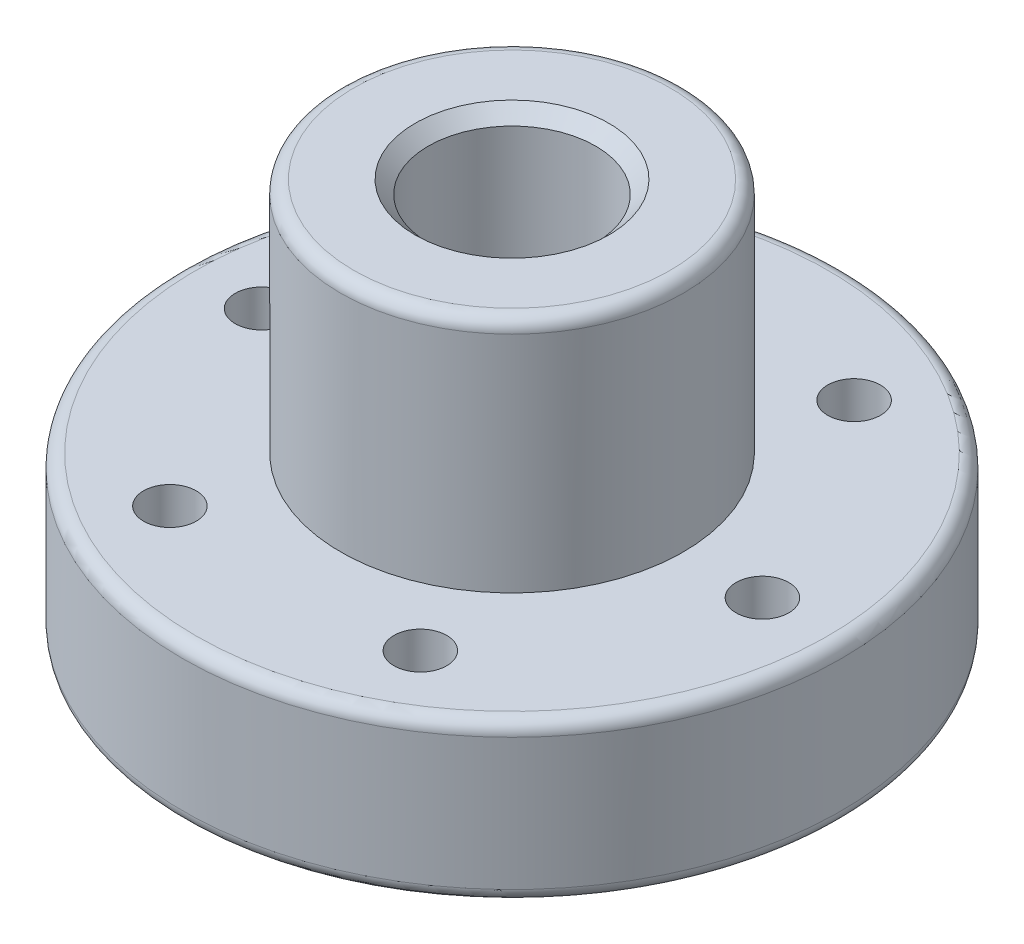
SolidWorks part; units mm, degrees
material "AISI 1035 Acier (SS)"
ref_plane "Plan de face" through (0, 0, 0) normal (0, 0, 1) x (1, 0, 0)
ref_plane "Plan de dessus" through (0, 0, 0) normal (0, 1, 0) x (1, 0, 0)
ref_plane "Plan de droite" through (0, 0, 0) normal (1, 0, 0) x (0, 0, -1)
sketch "Esquisse1" plane through (0, 0, 0) normal (0, 0, 1) x (1, 0, 0)
  line L0 (6.5, 15) -> (6.5, 6)
  line L1 (6.5, 6) -> (12.5, 6)
  line L2 (12.5, 6) -> (12.5, 0)
  line L9 (6.5, 15) -> (3.175, 15)
  line L10 (3.175, 15) -> (3.175, 0)
  line L11 (12.5, 0) -> (3.175, 0)
  line L12 (0, 0) -> (0, 15) construction
  dimension "D1" = 12.5
  dimension "D2" = 6
  dimension "D3" = 15
  dimension "D4" = 3.175
  dimension "D5" = 6
  dimension "D6" = 9.325
revolve "Révolution2" add sketch "Esquisse1" angle 360 about L12
sketch "Esquisse3" plane through (0, 6, 0) normal (0, 1, 0) x (1, 0, 0)
  line L0 (0, 0) -> (9.5, 0) construction
  circle A0 centre (9.5, 0) radius 1
  circle A2 centre (0, 0) radius 12.5 construction
  circle A3 centre (0, 0) radius 6.5 construction
  point P7 (6.5, 0)
  point P8 (12.5, 0)
  point P19 (0, 0)
  point P23 (0, -4.027)
  point P24 (0.0457, -3.8672)
  dimension "D1" = 2
  dimension "D3" = 3
  dimension "D2" = 3
extrude "Enlèv. mat.-Extru.1" cut sketch "Esquisse3" against normal through all
pattern_circular "Répétition circulaire1" count 6 over 360 about axis through (0, 0, 0) along (0, 1, 0) of "Enlèv. mat.-Extru.1"
fillet "Congé1" radius 0.5 3 edges at (0, 15, -6.5) (0, 0, -12.5) (0, 6, -12.5)
chamfer "Chanfrein1" distance 0.5 angle 45 2 edges at (0, 0, -3.175) (0, 15, -3.175)
